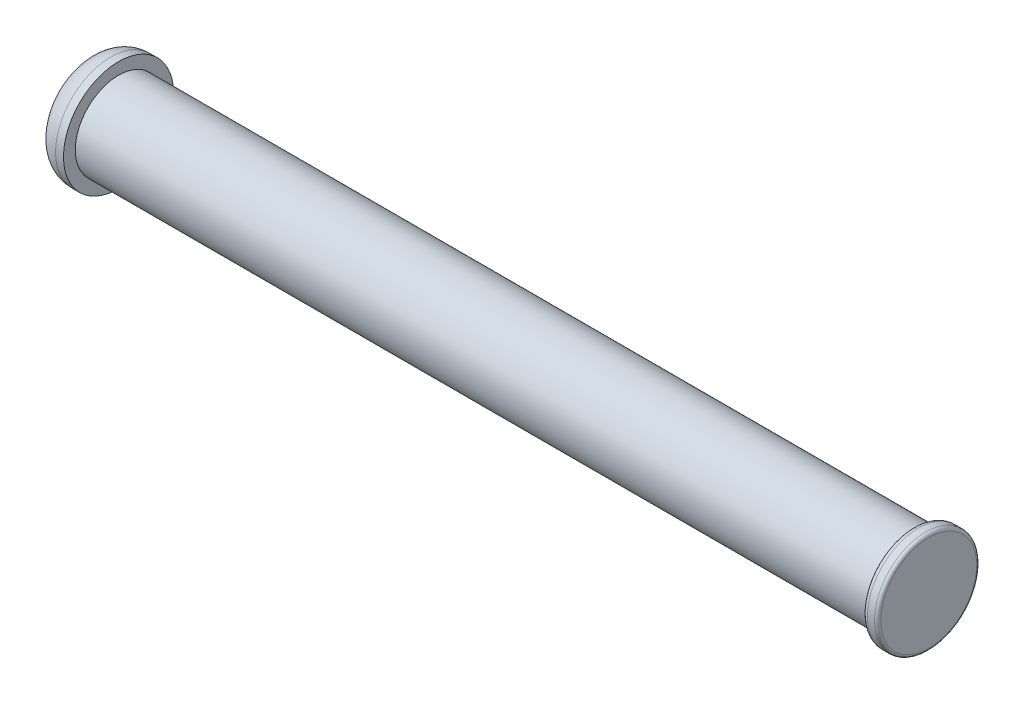
SolidWorks part; units mm, degrees
material "Stainless Steel (ferritic)"
ref_plane "Front Plane" through (0, 0, 0) normal (0, 0, 1) x (1, 0, 0)
ref_plane "Top Plane" through (0, 0, 0) normal (0, 1, 0) x (1, 0, 0)
ref_plane "Right Plane" through (0, 0, 0) normal (1, 0, 0) x (0, 0, -1)
sketch "Sketch1" plane through (0, 0, 0) normal (1, 0, 0) x (0, 0, -1)
  circle A0 centre (0, 0) radius 3.5
  dimension "D1" = 7
extrude "Boss-Extrude1" add sketch "Sketch1" along normal blind 2
sketch "Sketch2" plane through (2, 0, 0) normal (1, 0, 0) x (0, 0, -1)
  circle A0 centre (0, 0) radius 2.75
  dimension "D1" = 5.5
extrude "Boss-Extrude2" add sketch "Sketch2" along normal blind 50.5
sketch "Sketch3" plane through (52.5, 0, 0) normal (1, 0, 0) x (0, 0, -1)
  circle A0 centre (0, 0) radius 3.25
  dimension "D1" = 6.5
extrude "Boss-Extrude3" add sketch "Sketch3" along normal blind 1
fillet "Fillet1" radius 1.5 1 edges at (0, 0, -3.5)
fillet "Fillet2" radius 0.35 1 edges at (52.5, 0, -3.25)
fillet "Fillet3" radius 0.2 1 edges at (53.5, 0, -3.25)
